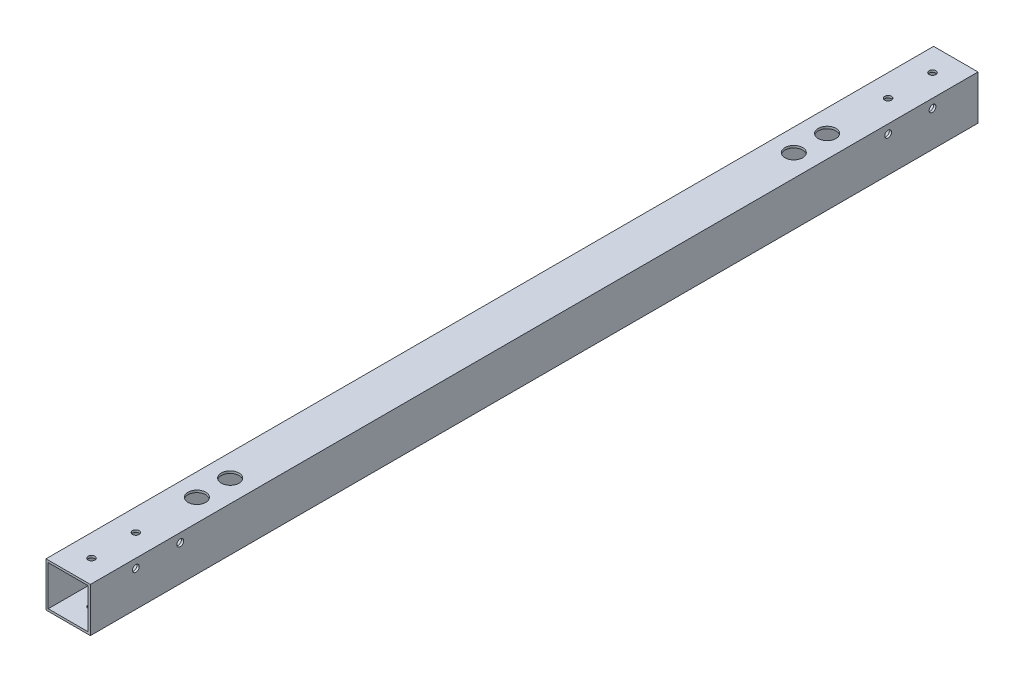
SolidWorks part; units mm, degrees
ref_plane "前视基准面" through (0, 0, 0) normal (0, 0, 1) x (1, 0, 0)
ref_plane "上视基准面" through (0, 0, 0) normal (0, 1, 0) x (1, 0, 0)
ref_plane "右视基准面" through (0, 0, 0) normal (1, 0, 0) x (0, 0, -1)
other "Configuration Table"
sketch "草图1" plane through (0, 0, 0) normal (0, 0, 1) x (1, 0, 0)
  line L1 (-10, -10) -> (10, -10)
  line L2 (-10, -10) -> (-10, 10)
  line L3 (-10, 10) -> (10, 10)
  line L4 (10, -10) -> (10, 10)
  line L5 (-10, -10) -> (10, 10) construction
  line L6 (-10, 10) -> (10, -10) construction
  point P0 (0, 0)
  dimension "D1" = 20
  dimension "D2" = 20
extrude "凸台-拉伸1" add sketch "草图1" along normal mid plane 400
sketch "草图2" plane through (0, 0, 0) normal (0, 0, 1) x (1, 0, 0)
  line L8 (9, -9) -> (9, 9)
  line L9 (9, 9) -> (-9, 9)
  line L10 (-9, 9) -> (-9, -9)
  line L11 (-9, -9) -> (9, -9)
  line L12 (9, -9) -> (9, 9)
  line L13 (9, 9) -> (-9, 9)
  line L14 (-9, 9) -> (-9, -9)
  line L15 (-9, -9) -> (9, -9)
  dimension "D1" = 1
extrude "切除-拉伸1" cut sketch "草图2" against normal through all both and the other way through all
sketch "草图3" plane through (0, 10, 0) normal (0, 1, 0) x (1, 0, 0)
  line L0 (10, -200) -> (-10, -200) construction
  line L2 (10, -200) -> (10, 200) construction
  circle A0 centre (0, -189.5) radius 1.525
  circle A1 centre (0, -169.5) radius 1.525
  dimension "D1" = 3.05
  dimension "D2" = 20
  dimension "D3" = 10.5
  dimension "D4" = 10
extrude "切除-拉伸2" cut sketch "草图3" against normal through all both and the other way through all
mirror "镜向1" about plane through (0, 0, 0) normal (0, 0, 1) of "切除-拉伸2"
sketch "草图4" plane through (10, 0, 0) normal (1, 0, 0) x (0, 0, -1)
  line L4 (200, -10) -> (200, 10)
  line L5 (200, 10) -> (-200, 10)
  line L6 (-200, 10) -> (-200, -10)
  line L7 (-200, -10) -> (200, -10)
  line L8 (200, -10) -> (200, 10)
  line L9 (200, 10) -> (-200, 10)
  line L10 (-200, 10) -> (-200, -10)
  line L11 (-200, -10) -> (200, -10)
  circle A0 centre (-179.5, 6) radius 1.525
  circle A1 centre (-159.5, 6) radius 1.525
  circle A2 centre (-179.5, 6) radius 1.25 construction
  circle A3 centre (-159.5, 6) radius 1.25 construction
  dimension "D2" = 3.05
  dimension "D1" = 0
extrude "切除-拉伸3" cut sketch "草图4" against normal through all both contours A0 | A1
sketch "草图5" plane through (0, -10, 0) normal (0, -1, 0) x (1, 0, 0)
  line L0 (10, 200) -> (10, -200) construction
  line L1 (-10, 200) -> (10, 200) construction
  circle A0 centre (0, 142) radius 2.025
  circle A1 centre (0, 127) radius 2.025
  dimension "D1" = 15
  dimension "D2" = 4.05
  dimension "D3" = 10
  dimension "D4" = 10
  dimension "D5" = 58
extrude "切除-拉伸4" cut sketch "草图5" against normal through all both
sketch "草图8" plane through (0, 10, 0) normal (0, 1, 0) x (1, 0, 0)
  circle A0 centre (0, -127) radius 4
  circle A1 centre (0, -142) radius 4
  dimension "D1" = 8
extrude "切除-拉伸5" cut sketch "草图8" against normal blind 3
mirror "镜向2" about plane through (0, 0, 0) normal (0, 0, 1) of "切除-拉伸5", "切除-拉伸4"
mirror "镜向3" about plane through (0, 0, 0) normal (0, 0, 1) of "切除-拉伸3"
